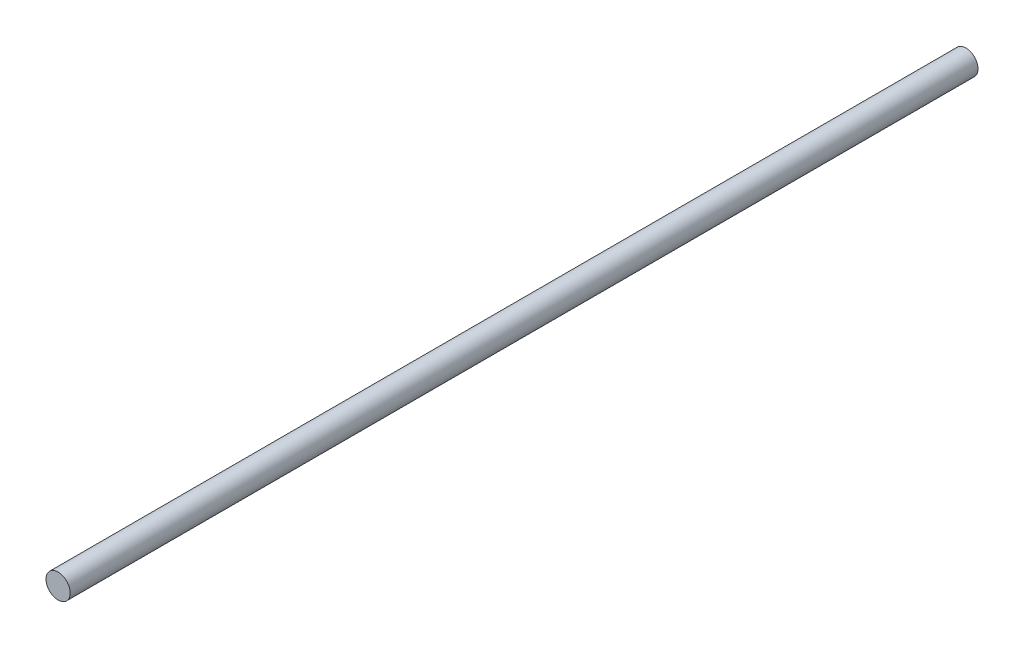
SolidWorks part; units mm, degrees
ref_plane "Plan de face" through (0, 0, 0) normal (0, 0, 1) x (1, 0, 0)
ref_plane "Plan de dessus" through (0, 0, 0) normal (0, 1, 0) x (1, 0, 0)
ref_plane "Plan de droite" through (0, 0, 0) normal (1, 0, 0) x (0, 0, -1)
sketch "Esquisse1" plane through (0, 0, 0) normal (0, 0, 1) x (1, 0, 0)
  circle A0 centre (0, 0) radius 4
  dimension "D1" = 8
extrude "Boss.-Extru.1" add sketch "Esquisse1" along normal blind 300
